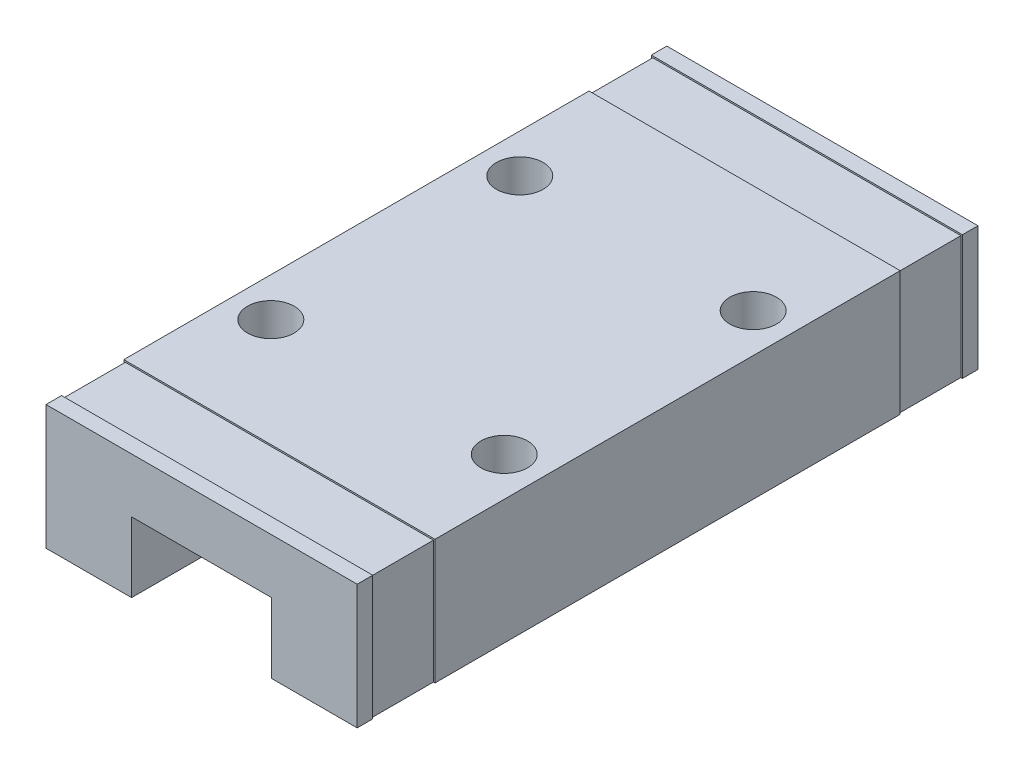
SolidWorks part; units mm, degrees
material "Plain Carbon Steel"
ref_plane "Front Plane" through (0, 0, 0) normal (0, 0, 1) x (1, 0, 0)
ref_plane "Top Plane" through (0, 0, 0) normal (0, 1, 0) x (1, 0, 0)
ref_plane "Right Plane" through (0, 0, 0) normal (1, 0, 0) x (0, 0, -1)
sketch "Sketch1" plane through (0, 0, 0) normal (0, 0, 1) x (1, 0, 0)
  line L0 (10, 8) -> (10, 0) construction
  line L1 (0, 0) -> (5.5, 0)
  line L2 (0, 0) -> (0, 8)
  line L3 (0, 8) -> (20, 8)
  line L4 (20, 0) -> (20, 8)
  line L5 (14.5, 0) -> (20, 0)
  line L7 (5.5, 0) -> (5.5, 4.5)
  line L8 (5.5, 4.5) -> (14.5, 4.5)
  line L9 (14.5, 0) -> (14.5, 4.5)
  line L10 (14.5, 4.5) -> (5.5, 4.5)
  line L11 (14.5, 4.5) -> (14.5, -2) construction
  line L12 (14.5, -2) -> (5.5, -2) construction
  line L13 (5.5, 4.5) -> (5.5, -2) construction
  dimension "D1" = 20
  dimension "D2" = 10
  dimension "D3" = 4.5
  dimension "D4" = 4.5
  dimension "D5" = 2
  dimension "D6" = 6.5
  dimension "D7" = 10
extrude "Boss-Extrude1" add sketch "Sketch1" along normal blind 39.9 contours L9 L5 L4 L3 L2 L1 L7 L8
sketch "Sketch2" plane through (0, 8, 0) normal (0, 1, 0) x (1, 0, 0)
  line L0 (0, -39.9) -> (0, 0) construction
  line L1 (0, -1) -> (20, -1)
  line L2 (0, -1) -> (0, -5)
  line L3 (0, -5) -> (20, -5)
  line L4 (20, -1) -> (20, -5)
  line L5 (20, -39.9) -> (20, 0) construction
  line L6 (0, 0) -> (20, 0) construction
  line L7 (0, -38.9) -> (20, -38.9)
  line L8 (0, -38.9) -> (0, -34.9)
  line L9 (0, -34.9) -> (20, -34.9)
  line L10 (20, -38.9) -> (20, -34.9)
  line L11 (0, -39.9) -> (20, -39.9) construction
  dimension "D1" = 29.9
  dimension "D2" = 1
  dimension "D3" = 1
extrude "Cut-Extrude1" cut sketch "Sketch2" against normal blind 0.1
sketch "Sketch3" plane through (0, 0, 0) normal (-1, 0, 0) x (0, 0, 1)
  line L0 (39.9, 0) -> (0, 0) construction
  line L1 (5, 7.9) -> (1, 7.9)
  line L2 (5, 7.9) -> (5, 0)
  line L3 (5, 0) -> (1, 0)
  line L4 (1, 7.9) -> (1, 0)
  line L5 (0, 0) -> (0, 8) construction
  line L6 (34.9, 7.9) -> (38.9, 7.9)
  line L7 (34.9, 7.9) -> (34.9, 0)
  line L8 (34.9, 0) -> (38.9, 0)
  line L9 (38.9, 7.9) -> (38.9, 0)
  line L10 (39.9, 0) -> (39.9, 8) construction
  dimension "D1" = 1
  dimension "D2" = 1
extrude "Cut-Extrude2" cut sketch "Sketch3" against normal blind 0.1
sketch "Sketch4" plane through (20, 0, 0) normal (1, 0, 0) x (0, 0, -1)
  line L0 (-39.9, 0) -> (0, 0) construction
  line L1 (-34.9, 7.9) -> (-38.9, 7.9)
  line L2 (-34.9, 7.9) -> (-34.9, 0)
  line L3 (-34.9, 0) -> (-38.9, 0)
  line L4 (-38.9, 7.9) -> (-38.9, 0)
  line L5 (-5, 7.9) -> (-1, 7.9)
  line L6 (-5, 7.9) -> (-5, 0)
  line L7 (-5, 0) -> (-1, 0)
  line L8 (-1, 7.9) -> (-1, 0)
extrude "Cut-Extrude3" cut sketch "Sketch4" against normal blind 0.1
sketch "Sketch5" plane through (0, 8, 0) normal (0, 1, 0) x (1, 0, 0)
  line L0 (0, -34.9) -> (0, -5) construction
  line L1 (2.5, -11.95) -> (17.5, -11.95) construction
  line L2 (2.5, -11.95) -> (2.5, -27.95) construction
  line L3 (2.5, -27.95) -> (17.5, -27.95) construction
  line L4 (17.5, -11.95) -> (17.5, -27.95) construction
  line L5 (0.1, -5) -> (19.9, -5) construction
  circle A0 centre (2.5, -11.95) radius 1.5
  circle A1 centre (17.5, -11.95) radius 1.5
  circle A2 centre (2.5, -27.95) radius 1.5
  circle A3 centre (17.5, -27.95) radius 1.5
  dimension "D5" = 3
  dimension "D1" = 15
  dimension "D2" = 16
  dimension "D3" = 2.5
  dimension "D4" = 6.95
extrude "Cut-Extrude4" cut sketch "Sketch5" against normal blind 3
